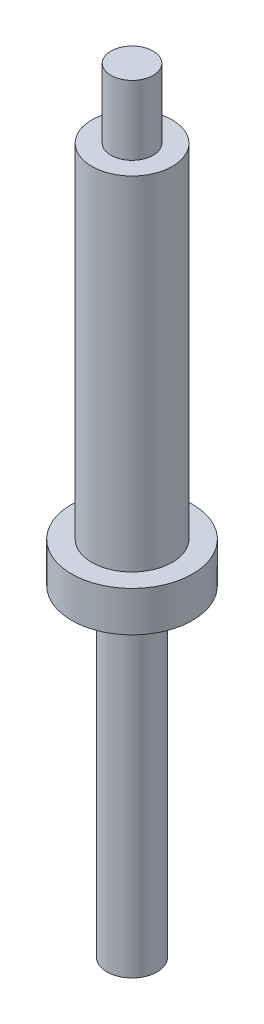
SolidWorks part; units mm, degrees
ref_plane "Front Plane" through (0, 0, 0) normal (0, 0, 1) x (1, 0, 0)
ref_plane "Top Plane" through (0, 0, 0) normal (0, 1, 0) x (1, 0, 0)
ref_plane "Right Plane" through (0, 0, 0) normal (1, 0, 0) x (0, 0, -1)
sketch "Sketch1" plane through (0, 0, 0) normal (0, 0, 1) x (1, 0, 0)
  line L0 (0, 0) -> (0, 79.052) construction
  line L1 (0, 0) -> (1.9812, 0)
  line L2 (1.9812, 0) -> (1.9812, 25.4)
  line L3 (1.9812, 25.4) -> (3.175, 25.4)
  line L4 (3.175, 25.4) -> (3.175, 55.626)
  line L5 (3.175, 55.626) -> (1.6637, 55.626)
  line L6 (1.6637, 55.626) -> (1.6637, 61.087)
  line L7 (1.6637, 61.087) -> (0, 61.087)
  line L11 (0, 61.087) -> (0, 0)
  dimension "D1" = 25.4
  dimension "D2" = 30.226
  dimension "D3" = 5.461
  dimension "D8" = 3.3274
  dimension "D9" = 6.35
  dimension "D10" = 3.9624
revolve "Revolve1" add sketch "Sketch1" angle 360 about L0
sketch "Sketch2" plane through (0, 25.4, 0) normal (0, -1, 0) x (1, 0, 0)
  circle A0 centre (0, 0) radius 4.7625
  dimension "D1" = 9.525
extrude "Boss-Extrude1" add sketch "Sketch2" against normal blind 3.175
sketch "Sketch3" plane through (0, 28.575, 0) normal (0, 1, 0) x (1, 0, 0)
  circle A0 centre (0, 0) radius 5.5626
  circle A1 centre (0, 0) radius 3.175
  dimension "D1" = 6.35
  dimension "D2" = 11.1252
extrude "Boss-Extrude2- Rubber Post Sleeve" [suppressed] add sketch "Sketch3" along normal blind 25.4
